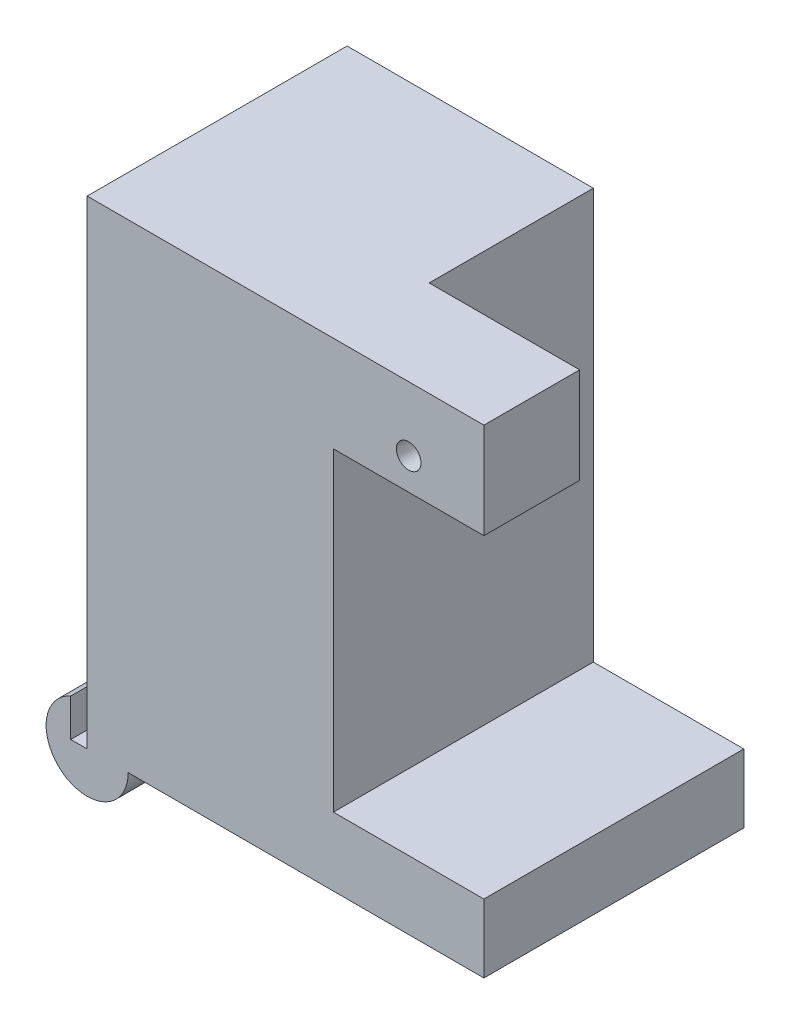
SolidWorks part; units mm, degrees
ref_plane "Front Plane" through (0, 0, 0) normal (0, 0, 1) x (1, 0, 0)
ref_plane "Top Plane" through (0, 0, 0) normal (0, 1, 0) x (1, 0, 0)
ref_plane "Right Plane" through (0, 0, 0) normal (1, 0, 0) x (0, 0, -1)
sketch "Sketch1" plane through (0, 0, 0) normal (0, 1, 0) x (1, 0, 0)
  line L1 (-10.3062, 7.9438) -> (7.6938, 7.9438)
  line L2 (-10.3062, 7.9438) -> (-10.3062, -11.0562)
  line L3 (-10.3062, -11.0562) -> (7.6938, -11.0562)
  line L4 (7.6938, 7.9438) -> (7.6938, -11.0562)
  dimension "D1" = 18
  dimension "D2" = 19
extrude "Boss-Extrude1" add sketch "Sketch1" along normal blind 35
sketch "Sketch2" plane through (7.6938, 0, 0) normal (1, 0, 0) x (0, 0, -1)
  line L0 (-11.0562, 35) -> (-11.0562, 0) construction
  line L1 (7.9438, 0) -> (-11.0562, 0)
  line L2 (7.9438, 0) -> (7.9438, 5)
  line L3 (7.9438, 5) -> (-11.0562, 5)
  line L4 (-11.0562, 0) -> (-11.0562, 5)
  line L5 (7.9438, 35) -> (7.9438, 0) construction
  line L6 (-11.0562, 35) -> (7.9438, 35)
  line L7 (-11.0562, 35) -> (-11.0562, 28)
  line L8 (-11.0562, 28) -> (7.9438, 28)
  line L9 (7.9438, 35) -> (7.9438, 28)
  dimension "D1" = 23
  dimension "D2" = 5
extrude "Boss-Extrude2" add sketch "Sketch2" along normal blind 11
sketch "Sketch3" plane through (18.6938, 0, 0) normal (1, 0, 0) x (0, 0, -1)
  line L0 (7.9438, 35) -> (-11.0562, 35) construction
  line L1 (-4.0562, 35) -> (7.9438, 35)
  line L2 (-4.0562, 35) -> (-4.0562, 28)
  line L3 (-4.0562, 28) -> (7.9438, 28)
  line L4 (7.9438, 35) -> (7.9438, 28)
  line L5 (-11.0562, 35) -> (-11.0562, 28) construction
  dimension "D2" = 7
extrude "Cut-Extrude1" cut sketch "Sketch3" against normal up to surface (11 mm away) up to face at (7.6938, 22.25, -0.8188)
sketch "Sketch7" plane through (0, 0, 0) normal (0, -1, 0) x (1, 0, 0)
  line L0 (-10.3062, 11.0562) -> (18.6938, 11.0562) construction
  line L1 (-10.3062, -7.9438) -> (-7.3062, -7.9438)
  line L2 (-10.3062, -7.9438) -> (-10.3062, 11.0562)
  line L3 (-10.3062, 11.0562) -> (-7.3062, 11.0562)
  line L4 (-7.3062, -7.9438) -> (-7.3062, 11.0562)
  dimension "D1" = 3
revolve "Revolve2" add sketch "Sketch7" angle 360 about L2
sketch "Sketch9" plane through (0, 0, 0) normal (0, -1, 0) x (1, 0, 0)
  line L0 (-10.3062, -7.9438) -> (-10.3062, 11.0562) construction
  line L1 (18.6938, -7.9438) -> (-20.3062, -7.9438)
  line L2 (18.6938, -7.9438) -> (18.6938, -1.9438)
  line L3 (18.6938, -1.9438) -> (-20.3062, -1.9438)
  line L4 (-20.3062, -7.9438) -> (-20.3062, -1.9438)
  dimension "D1" = 6
  dimension "D2" = 10
extrude "Cut-Extrude3" cut sketch "Sketch9" along normal through all contours L2 L3 L4 L1
sketch "Sketch10" plane through (-10.3062, 0, 0) normal (-1, 0, 0) x (0, 0, 1)
  line L1 (-7.9438, 35) -> (-1.9438, 35)
  line L2 (-7.9438, 35) -> (-7.9438, 0)
  line L3 (-7.9438, 0) -> (-1.9438, 0)
  line L4 (-1.9438, 35) -> (-1.9438, 0)
  line L6 (-1.9438, 0) -> (-1.9438, -3) construction
  line L7 (11.0562, 0) -> (-7.9438, 0) construction
extrude "Cut-Extrude4" cut sketch "Sketch10" along normal through all
sketch "Sketch11" plane through (0, 35, 0) normal (0, 1, 0) x (1, 0, 0)
  line L0 (7.6938, 7.9438) -> (-10.3062, 7.9438) construction
  line L1 (-10.3062, -11.0562) -> (-11.5062, -11.0562)
  line L2 (-10.3062, -11.0562) -> (-10.3062, 7.9438)
  line L3 (-10.3062, 7.9438) -> (-11.5062, 7.9438)
  line L4 (-11.5062, -11.0562) -> (-11.5062, 7.9438)
  dimension "D1" = 1.2
extrude "Cut-Extrude5" cut sketch "Sketch11" against normal up to surface (35 mm away) up to face at (0.3605, 0, 0.3895)
sketch "Sketch12" plane through (-10.3062, 0, 0) normal (-1, 0, 0) x (0, 0, 1)
  line L0 (-7.9438, 35) -> (-7.9438, 0) construction
  line L1 (-7.9438, 0) -> (-1.9438, 0) construction
  circle A0 centre (-3.9438, 4) radius 1.4
  point P4 (-4.9438, 0)
  dimension "D1" = 2.8
  dimension "D2" = 4
  dimension "D3" = 4
extrude "Cut-Extrude6" cut sketch "Sketch12" against normal blind 5
sketch "Sketch13" plane through (0, 0, 11.0562) normal (0, 0, 1) x (1, 0, 0)
  line L0 (18.6938, 28) -> (7.6938, 28) construction
  circle A0 centre (13.1938, 30.3) radius 0.9
  dimension "D1" = 1.8
  dimension "D2" = 2.3
  dimension "D3" = 5.5
extrude "Cut-Extrude7" cut sketch "Sketch13" against normal through all contours A0
